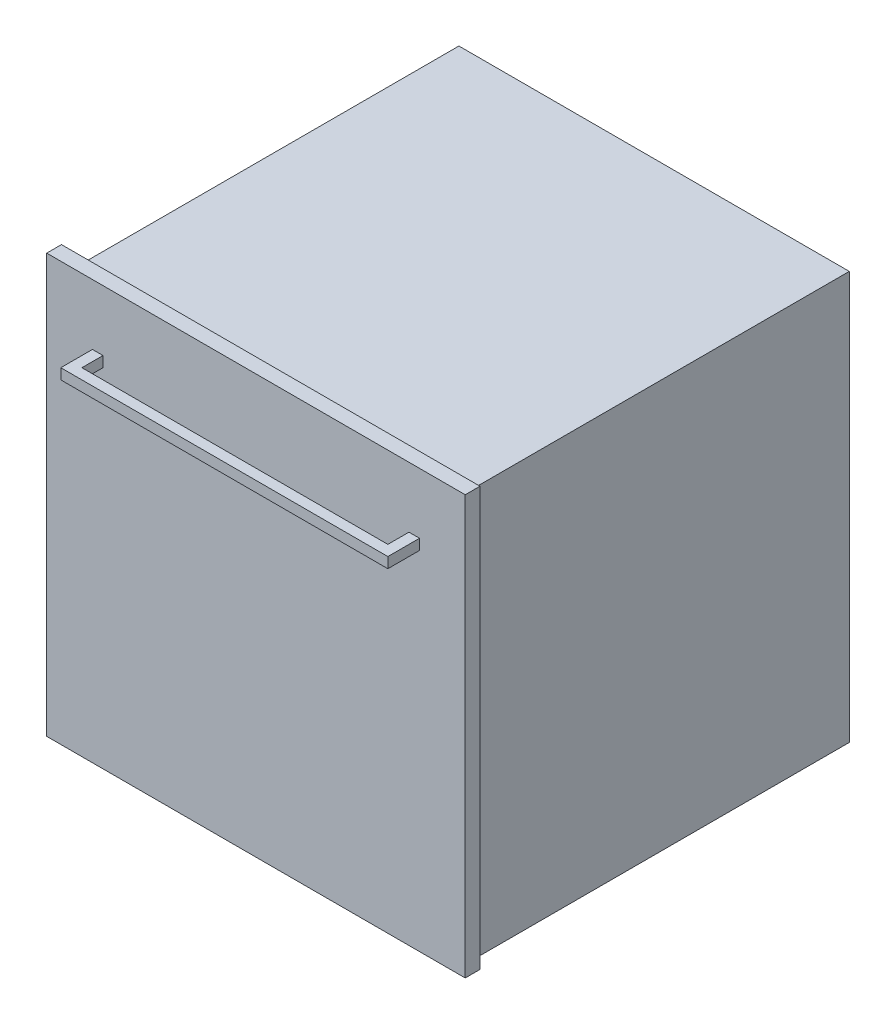
SolidWorks part; units mm, degrees
ref_plane "Спереди" through (0, 0, 0) normal (0, 0, 1) x (1, 0, 0)
ref_plane "Сверху" through (0, 0, 0) normal (0, 1, 0) x (1, 0, 0)
ref_plane "Справа" through (0, 0, 0) normal (1, 0, 0) x (0, 0, -1)
sketch "Эскиз1" plane through (0, 0, 0) normal (0, 1, 0) x (1, 0, 0)
  line L1 (277.5, -272.5) -> (-277.5, -272.5)
  line L2 (277.5, -272.5) -> (277.5, 272.5)
  line L3 (277.5, 272.5) -> (-277.5, 272.5)
  line L4 (-277.5, -272.5) -> (-277.5, 272.5)
  line L5 (277.5, -272.5) -> (-277.5, 272.5) construction
  line L6 (277.5, 272.5) -> (-277.5, -272.5) construction
  point P0 (0, 0)
  dimension "D1" = 545
  dimension "D2" = 555
extrude "Бобышка-Вытянуть1" add sketch "Эскиз1" along normal blind 580
sketch "Эскиз2" plane through (0, 0, 272.5) normal (0, 0, 1) x (1, 0, 0)
  line L0 (0, 0) -> (0, 300.5) construction
  line L1 (297.5, 3) -> (-297.5, 3)
  line L2 (297.5, 3) -> (297.5, 598)
  line L3 (297.5, 598) -> (-297.5, 598)
  line L4 (-297.5, 3) -> (-297.5, 598)
  line L5 (297.5, 3) -> (-297.5, 598) construction
  line L6 (297.5, 598) -> (-297.5, 3) construction
  line L7 (-277.5, 0) -> (277.5, 0) construction
  line L8 (-277.5, 580) -> (277.5, 580) construction
  point P0 (0, 300.5)
  dimension "D1" = 595
  dimension "D2" = 595
  dimension "D3" = 18
  dimension "D4" = 3
extrude "Бобышка-Вытянуть2" add sketch "Эскиз2" along normal blind 21
sketch "Эскиз3" plane through (0, 0, 293.5) normal (0, 0, 1) x (1, 0, 0)
  line L0 (-225, 504.4134) -> (225, 504.4134) construction
  line L1 (-232.5, 511.9134) -> (-217.5, 511.9134)
  line L2 (-232.5, 511.9134) -> (-232.5, 496.9134)
  line L3 (-232.5, 496.9134) -> (-217.5, 496.9134)
  line L4 (-217.5, 511.9134) -> (-217.5, 496.9134)
  line L5 (-232.5, 511.9134) -> (-217.5, 496.9134) construction
  line L6 (-232.5, 496.9134) -> (-217.5, 511.9134) construction
  line L7 (217.5, 511.9134) -> (232.5, 511.9134)
  line L8 (217.5, 511.9134) -> (217.5, 496.9134)
  line L9 (217.5, 496.9134) -> (232.5, 496.9134)
  line L10 (232.5, 511.9134) -> (232.5, 496.9134)
  line L11 (217.5, 511.9134) -> (232.5, 496.9134) construction
  line L12 (217.5, 496.9134) -> (232.5, 511.9134) construction
  line L13 (0, 598) -> (0, 504.4134) construction
  line L14 (297.5, 598) -> (-297.5, 598) construction
  point P0 (-225, 504.4134)
  point P5 (225, 504.4134)
  dimension "D1" = 15
  dimension "D2" = 450
extrude "Бобышка-Вытянуть3" add sketch "Эскиз3" along normal blind 30
sketch "Эскиз4" plane through (0, 0, 323.5) normal (0, 0, 1) x (1, 0, 0)
  line L0 (-232.5, 496.9134) -> (-217.5, 496.9134) construction
  line L1 (-232.5, 511.9134) -> (-232.5, 496.9134) construction
  line L3 (-232.5, 496.9134) -> (232.5, 496.9134)
  line L4 (-232.5, 511.9134) -> (-232.5, 496.9134)
  line L7 (232.5, 496.9134) -> (232.5, 511.9134) construction
  line L8 (232.5, 511.9134) -> (217.5, 511.9134) construction
  line L10 (232.5, 496.9134) -> (232.5, 511.9134)
  line L11 (232.5, 511.9134) -> (-232.5, 511.9134)
extrude "Бобышка-Вытянуть4" add sketch "Эскиз4" along normal blind 15
